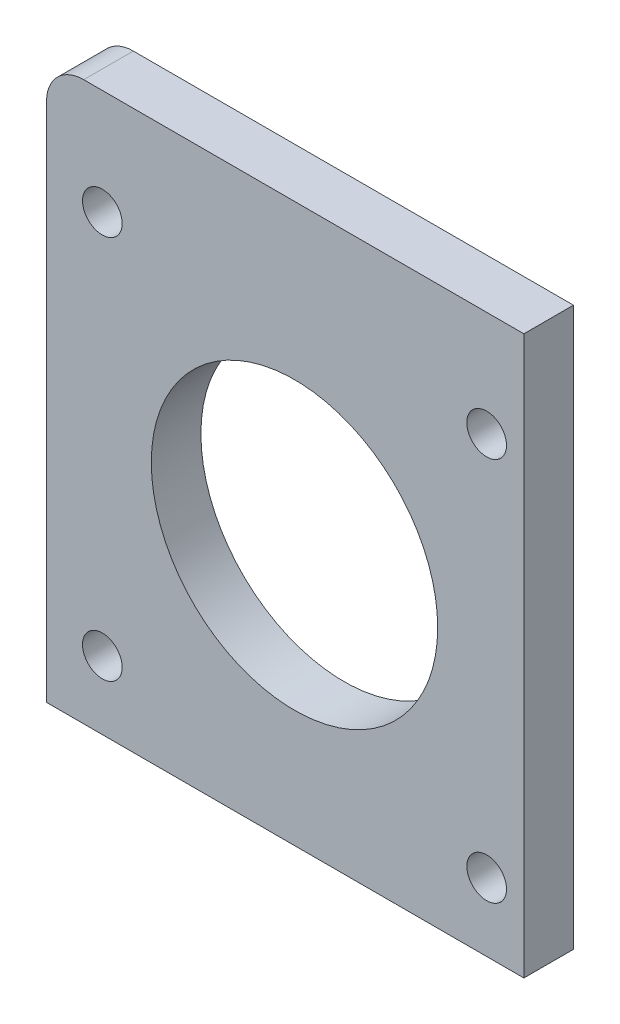
SolidWorks part; units mm, degrees
ref_plane "Front Plane" through (0, 0, 0) normal (0, 0, 1) x (1, 0, 0)
ref_plane "Top Plane" through (0, 0, 0) normal (0, 1, 0) x (1, 0, 0)
ref_plane "Right Plane" through (0, 0, 0) normal (1, 0, 0) x (0, 0, -1)
sketch "Sketch1" plane through (0, 0, 0) normal (0, 0, 1) x (1, 0, 0)
  line L4 (27.0711, -55.5949) -> (62.5711, -55.5949)
  line L5 (24.0711, -100.5949) -> (24.0711, -58.5949)
  line L6 (24.0711, -100.5949) -> (62.5711, -100.5949)
  line L7 (62.5711, -100.5949) -> (62.5711, -55.5949)
  arc A6 (27.0711, -55.5949) -> (24.0711, -58.5949) centre (27.0711, -58.5949) ccw
  circle A7 centre (28.5711, -64.0949) radius 1.6
  circle A8 centre (44.0711, -79.5949) radius 3
  circle A9 centre (59.5711, -64.0949) radius 1.6
  circle A10 centre (28.5711, -95.0949) radius 1.6
  circle A11 centre (59.5711, -95.0949) radius 1.6
extrude "Boss-Extrude1" add sketch "Sketch1" along normal blind 4
sketch "Sketch2" plane through (0, 0, 0) normal (0, 0, -1) x (-1, 0, 0)
  circle A0 centre (-44.0711, -79.5949) radius 11.5502
extrude "Cut-Extrude1" cut sketch "Sketch2" against normal blind 5
